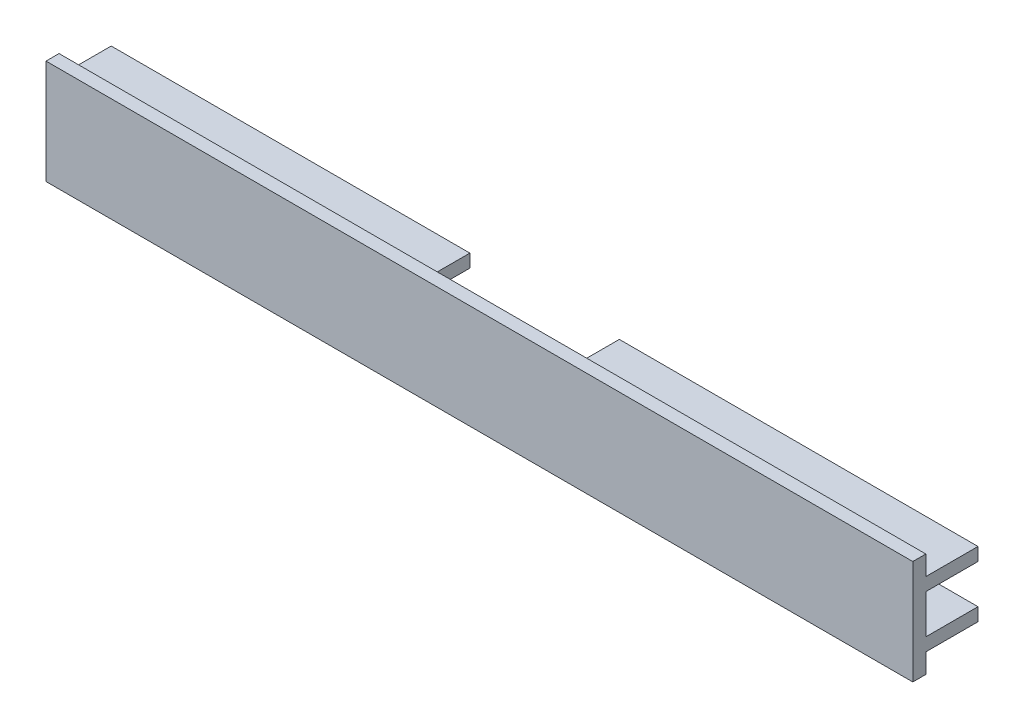
SolidWorks part; units mm, degrees
ref_plane "Front Plane" through (0, 0, 0) normal (0, 0, 1) x (1, 0, 0)
ref_plane "Top Plane" through (0, 0, 0) normal (0, 1, 0) x (1, 0, 0)
ref_plane "Right Plane" through (0, 0, 0) normal (1, 0, 0) x (0, 0, -1)
sketch "Sketch1" plane through (0, 0, 0) normal (1, 0, 0) x (0, 0, -1)
  line L0 (-3, 8) -> (-3, 5)
  line L1 (-5, 8) -> (-3, 8)
  line L2 (-5, 8) -> (-5, -8)
  line L3 (-5, -8) -> (-3, -8)
  line L4 (5, 5) -> (5, 3)
  line L5 (-5, 8) -> (5, -8) construction
  line L6 (-5, -8) -> (5, 8) construction
  line L7 (-3, 5) -> (5, 5)
  line L8 (5, 3) -> (-2, 3)
  line L9 (-2, 3) -> (-2, -3)
  line L10 (-2, -3) -> (5, -3)
  line L11 (5, -5) -> (-3, -5)
  line L12 (-3, -5) -> (-3, -8)
  line L13 (5, -3) -> (5, -5)
  point P0 (0, 0)
  dimension "D1" = 16
  dimension "D2" = 10
  dimension "D3" = 2
  dimension "D4" = 2
  dimension "D5" = 2
  dimension "D6" = 6
  dimension "D7" = 3
  dimension "D8" = 7
  dimension "D9" = 10
  dimension "D10" = 5
extrude "Extrude1" add sketch "Sketch1" along normal mid plane 132.92
sketch "Sketch2" plane through (-66.46, 0, 0) normal (-1, 0, 0) x (0, 0, 1)
  line L0 (2, 3) -> (3, 3)
  line L1 (3, 3) -> (3, -3)
  line L2 (3, -3) -> (2, -3)
  line L3 (2, -3) -> (2, 3)
  dimension "D1" = 1
extrude "Extrude2" cut sketch "Sketch2" against normal blind 56.5
sketch "Sketch3" plane through (66.46, 0, 0) normal (1, 0, 0) x (0, 0, -1)
  line L0 (-2, 3) -> (-3, 3)
  line L1 (-3, 3) -> (-3, -3)
  line L2 (-3, -3) -> (-2, -3)
  line L3 (-2, -3) -> (-2, 3) construction
  line L4 (-2, 3) -> (-2, -3)
  dimension "D1" = 1
extrude "Extrude3" cut sketch "Sketch3" against normal blind 56.5
sketch "Sketch4" plane through (0, 0, 2) normal (0, 0, -1) x (-1, 0, 0)
  line L0 (9.96, -3) -> (9.96, 3) construction
  line L1 (-9.96, -3) -> (-9.96, 3) construction
  line L2 (-9.96, 3) -> (-9.96, -3)
  line L3 (9.96, 3) -> (9.96, -3)
  arc A0 (9.96, 3) -> (9.96, -3) centre (9.96, 0) ccw
  arc A1 (-9.96, -3) -> (-9.96, 3) centre (-9.96, 0) ccw
extrude "Extrude4" cut sketch "Sketch4" against normal up to surface (1 mm away) up to face at (38.21, 0, 3)
sketch "Sketch5" plane through (0, 0, -5) normal (0, 0, -1) x (-1, 0, 0)
  line L0 (-66.46, 5) -> (66.46, 5) construction
  line L1 (-11.46, 5) -> (11.46, 5)
  line L2 (-11.46, 5) -> (-11.46, -5)
  line L3 (-11.46, -5) -> (11.46, -5)
  line L4 (11.46, 5) -> (11.46, -5)
  line L5 (-11.46, 5) -> (11.46, -5) construction
  line L6 (-11.46, -5) -> (11.46, 5) construction
  line L7 (-66.46, 3) -> (-66.46, 5) construction
  point P0 (0, 0)
  dimension "D1" = 55
extrude "Extrude5" cut sketch "Sketch5" against normal up to surface (7 mm away) up to face at (0, 0, 2)
